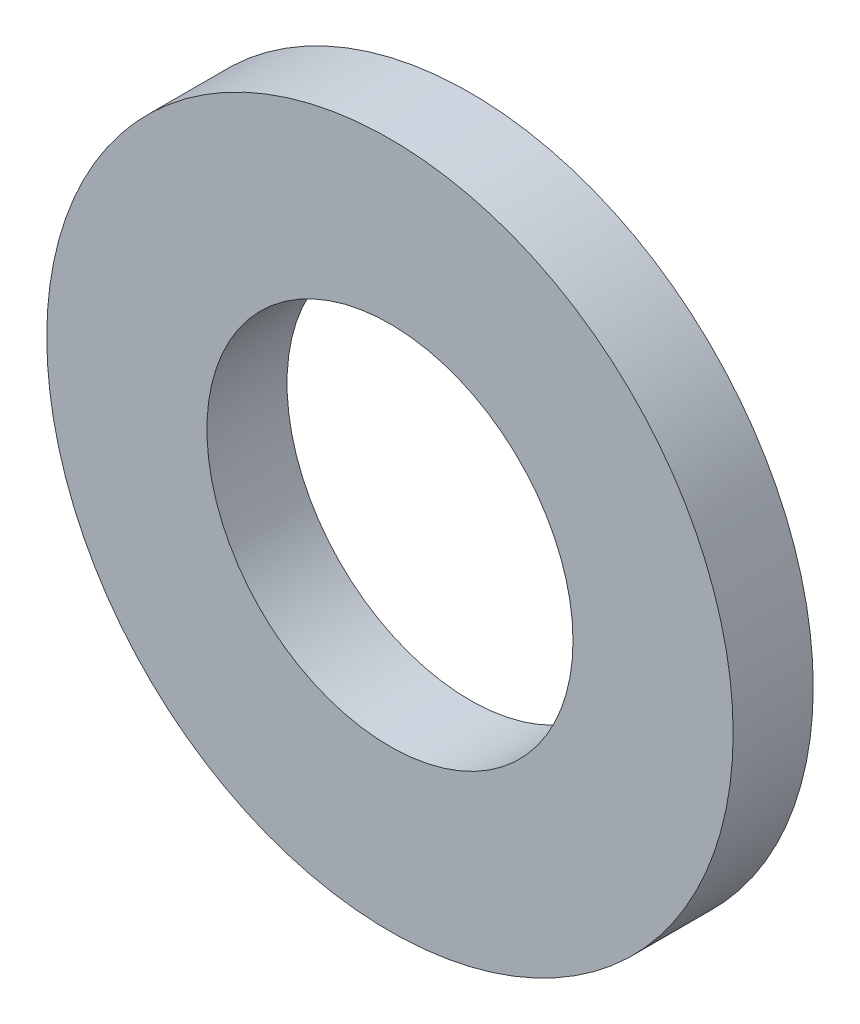
SolidWorks part; units mm, degrees
material "AISI 304"
ref_plane "Front Plane" through (0, 0, 0) normal (0, 0, 1) x (1, 0, 0)
ref_plane "Top Plane" through (0, 0, 0) normal (0, 1, 0) x (1, 0, 0)
ref_plane "Right Plane" through (0, 0, 0) normal (1, 0, 0) x (0, 0, -1)
sketch "Sketch1" plane through (0, 0, 0) normal (0, 0, 1) x (1, 0, 0)
  circle A0 centre (0, 0) radius 3.2
  circle A1 centre (0, 0) radius 6
  dimension "ID" = 6.4
  dimension "OD" = 12
extrude "Extrude1" add sketch "Sketch1" against normal blind 1.4
